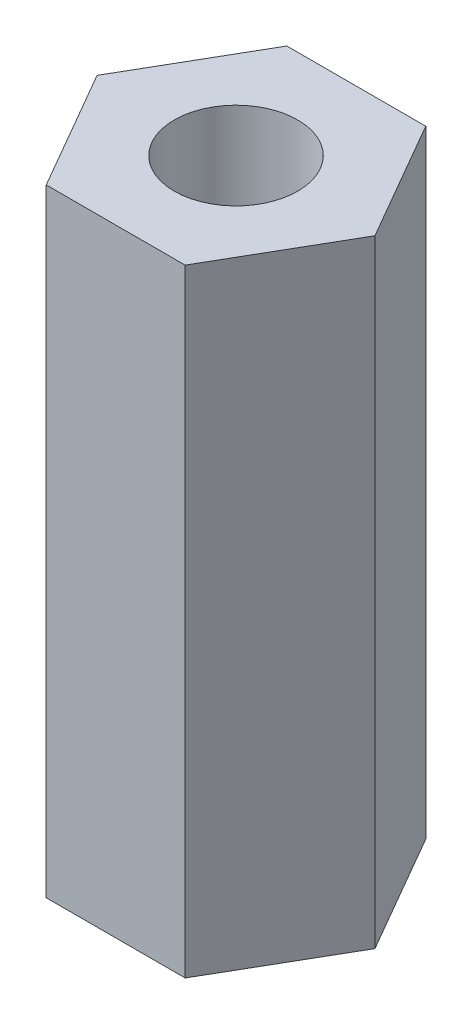
SolidWorks part; units mm, degrees
ref_plane "Front Plane" through (0, 0, 0) normal (0, 0, 1) x (1, 0, 0)
ref_plane "Top Plane" through (0, 0, 0) normal (0, 1, 0) x (1, 0, 0)
ref_plane "Right Plane" through (0, 0, 0) normal (1, 0, 0) x (0, 0, -1)
sketch "Sketch1" plane through (0, 0, 0) normal (0, 1, 0) x (1, 0, 0)
  line L1 (2.25, 0) -> (1.125, 1.9486)
  line L2 (1.125, 1.9486) -> (-1.125, 1.9486)
  line L3 (-1.125, 1.9486) -> (-2.25, 0)
  line L4 (-2.25, 0) -> (-1.125, -1.9486)
  line L5 (-1.125, -1.9486) -> (1.125, -1.9486)
  line L6 (1.125, -1.9486) -> (2.25, 0)
  circle A0 centre (0, 0) radius 1.9486 construction
  circle A1 centre (0, 0) radius 1
  dimension "D2" = 2
  dimension "D1" = 4.5
extrude "Boss-Extrude1" add sketch "Sketch1" along normal blind 10
